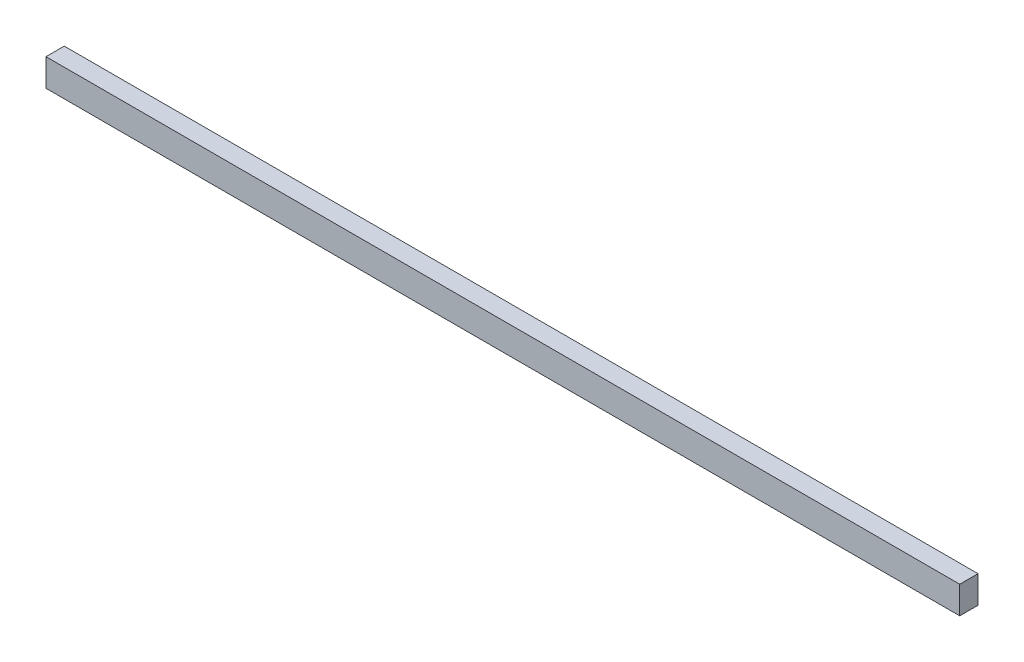
SolidWorks part; units mm, degrees
ref_plane "前视基准面" through (0, 0, 0) normal (0, 0, 1) x (1, 0, 0)
ref_plane "上视基准面" through (0, 0, 0) normal (0, 1, 0) x (1, 0, 0)
ref_plane "右视基准面" through (0, 0, 0) normal (1, 0, 0) x (0, 0, -1)
sketch "草图1" plane through (0, 0, 0) normal (0, 1, 0) x (1, 0, 0)
  line L1 (4.6561, -35.4062) -> (104.6561, -35.4062)
  line L2 (4.6561, -35.4062) -> (4.6561, -37.4062)
  line L3 (4.6561, -37.4062) -> (104.6561, -37.4062)
  line L4 (104.6561, -35.4062) -> (104.6561, -37.4062)
  dimension "D1" = 2
  dimension "D2" = 100
extrude "凸台-拉伸1" add sketch "草图1" along normal blind 3
